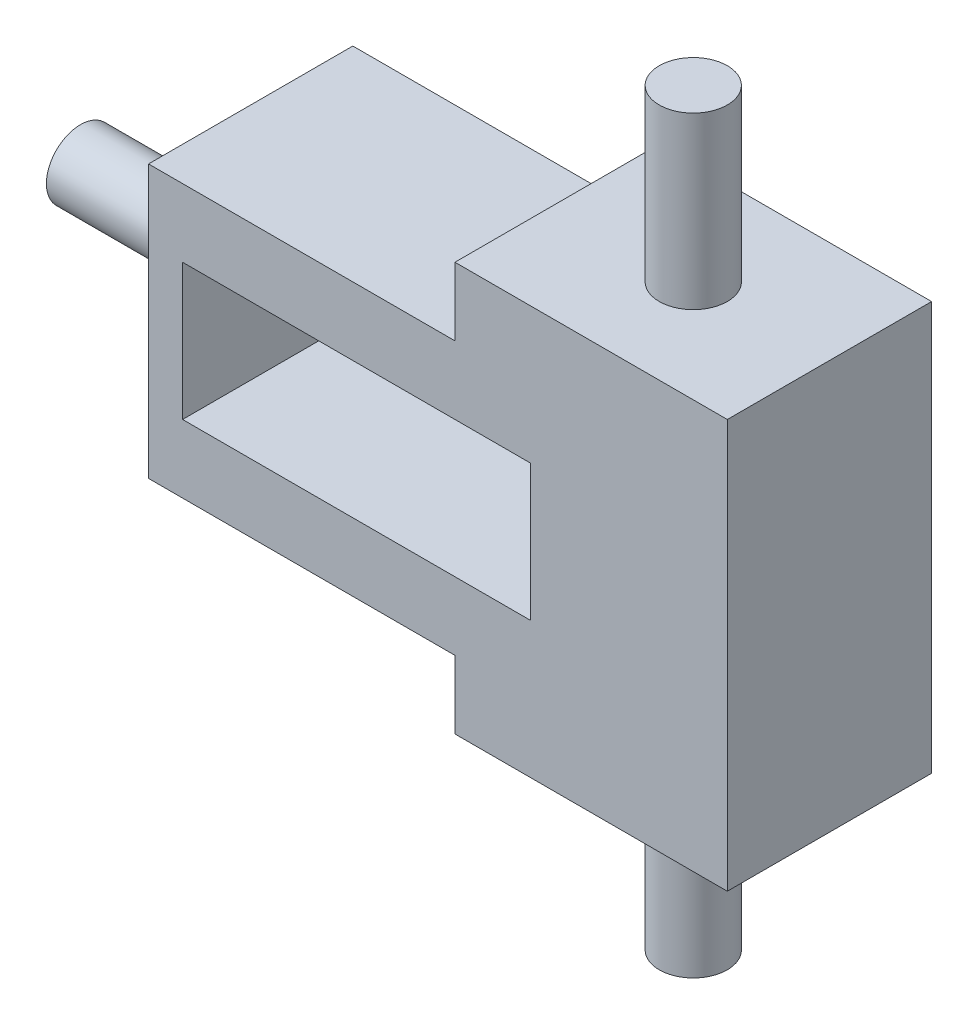
SolidWorks part; units mm, degrees
ref_plane "Alzado" through (0, 0, 0) normal (0, 0, 1) x (1, 0, 0)
ref_plane "Planta" through (0, 0, 0) normal (0, 1, 0) x (1, 0, 0)
ref_plane "Vista lateral" through (0, 0, 0) normal (1, 0, 0) x (0, 0, -1)
sketch "Croquis1" plane through (0, 0, 0) normal (0, 0, 1) x (1, 0, 0)
  line L2 (-2, 2) -> (2, 2)
  line L4 (2, -2) -> (-2, -2)
  line L6 (-2, 1) -> (-2, -1)
  line L11 (-2, -2) -> (-2.5, -2)
  line L12 (-2.5, -2) -> (-2.5, -0.4965)
  line L13 (-2.5, 2) -> (-2, 2)
  line L14 (-2.5, 0.5035) -> (-2.5, 2)
  line L15 (3.1064, 1) -> (3.1064, -1)
  line L18 (2, 2) -> (2, 3)
  line L19 (2, 3) -> (6, 3)
  line L20 (6, 3) -> (6, -3)
  line L21 (6, -3) -> (2, -3)
  line L22 (2, -3) -> (2, -2)
  line L23 (-2.5, 0.5035) -> (-2.5, -0.4965)
  line L24 (-2, 1) -> (3.1064, 1)
  line L25 (3.1064, -1) -> (-2, -1)
  point P0 (2, -2.5)
  dimension "D1" = 1
  dimension "D2" = 1
  dimension "D3" = 4.5
  dimension "D4" = 4
  dimension "D5" = 4
extrude "Saliente-Extruir1" add sketch "Croquis1" along normal blind 3
sketch "Croquis2" plane through (0, 3, 0) normal (0, 1, 0) x (1, 0, 0)
  circle A0 centre (4, -1.5) radius 0.5
  dimension "D1" = 1
extrude "Saliente-Extruir2" add sketch "Croquis2" along normal blind 2.5 and the other way blind 8.5
sketch "Croquis3" plane through (-2.5, 0, 0) normal (-1, 0, 0) x (0, 0, 1)
  circle A0 centre (1.5, 0) radius 0.5
  dimension "D1" = 1
extrude "Saliente-Extruir3" add sketch "Croquis3" along normal blind 2.5
